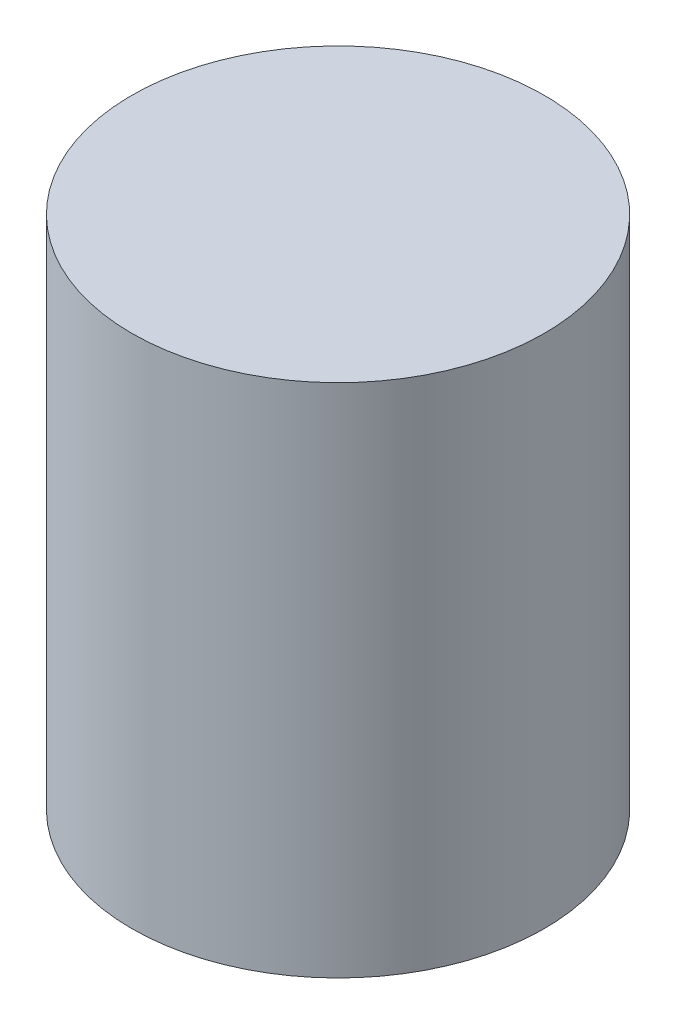
SolidWorks part; units mm, degrees
ref_plane "Front Plane" through (0, 0, 0) normal (0, 0, 1) x (1, 0, 0)
ref_plane "Top Plane" through (0, 0, 0) normal (0, 1, 0) x (1, 0, 0)
ref_plane "Right Plane" through (0, 0, 0) normal (1, 0, 0) x (0, 0, -1)
sketch "Sketch1" plane through (0, 0, 0) normal (0, 1, 0) x (1, 0, 0)
  circle A0 centre (0, 0) radius 10
  dimension "D1" = 20
extrude "Boss-Extrude1" add sketch "Sketch1" along normal blind 25
